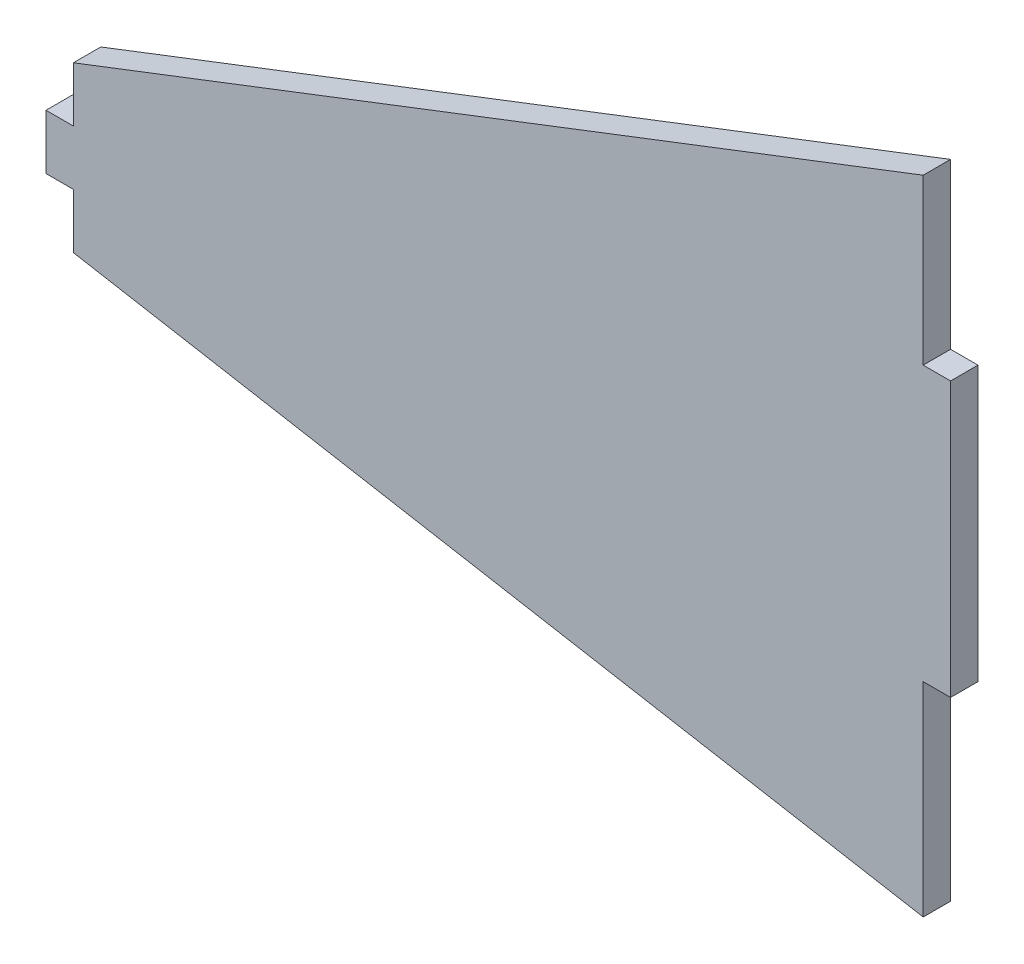
SolidWorks part; units mm, degrees
ref_plane "Front Plane" through (0, 0, 0) normal (0, 0, 1) x (1, 0, 0)
ref_plane "Top Plane" through (0, 0, 0) normal (0, 1, 0) x (1, 0, 0)
ref_plane "Right Plane" through (0, 0, 0) normal (1, 0, 0) x (0, 0, -1)
sketch "Sketch1" plane through (0, 0, 0) normal (0, 0, 1) x (1, 0, 0)
  line L0 (0, -9.525) -> (0, 9.525)
  line L5 (0, 9.525) -> (101.6, 48.6833)
  line L6 (101.6, 48.6833) -> (101.6, -27.5167)
  line L7 (101.6, -27.5167) -> (0, -9.525)
  line L8 (98.425, -26.9544) -> (98.425, 47.4596)
  line L10 (98.425, -3.3404) -> (101.6, -3.3404)
  line L11 (98.425, -3.3404) -> (98.425, 28.4096)
  line L12 (98.425, 28.4096) -> (101.6, 28.4096)
  line L13 (101.6, -3.3404) -> (101.6, 28.4096)
  line L14 (98.425, -3.3404) -> (101.6, 28.4096) construction
  line L15 (98.425, 28.4096) -> (101.6, -3.3404) construction
  point P4 (100.0125, 12.5346)
  dimension "D2" = 76.2
  dimension "D1" = 101.6
  dimension "D3" = 27.5167
  dimension "D4" = 19.05
  dimension "D5" = 3.175
  dimension "D6" = 31.75
  dimension "D9" = 19.05
extrude "Boss-Extrude2" add sketch "Sketch1" along normal blind 3.175
sketch "Sketch2" plane through (0, 0, 3.175) normal (0, 0, 1) x (1, 0, 0)
  line L0 (0, -9.525) -> (0, 9.525) construction
  line L1 (0, 3.175) -> (-3.175, 3.175)
  line L2 (0, 3.175) -> (0, -3.175)
  line L3 (0, -3.175) -> (-3.175, -3.175)
  line L4 (-3.175, 3.175) -> (-3.175, -3.175)
  line L6 (0, 9.525) -> (-3.175, 9.525) construction
  line L7 (0, 9.525) -> (0, -9.525) construction
  line L8 (0, -9.525) -> (-3.175, -9.525) construction
  line L9 (-3.175, 9.525) -> (-3.175, -9.525) construction
  line L10 (0, -2.413) -> (-3.175, -2.413) construction
  line L11 (0, -2.413) -> (0, 2.413) construction
  line L12 (0, 2.413) -> (-3.175, 2.413) construction
  line L13 (-3.175, -2.413) -> (-3.175, 2.413) construction
  point P10 (-3.175, 0)
  point P16 (-3.175, 0)
  point P17 (-3.175, 0)
  dimension "D1" = 3.175
  dimension "D2" = 19.05
  dimension "D3" = 4.826
  dimension "D4" = 6.35
extrude "Boss-Extrude3" add sketch "Sketch2" against normal up to surface (3.175 mm away) up to face at (74.6125, 8.8305, 0)
